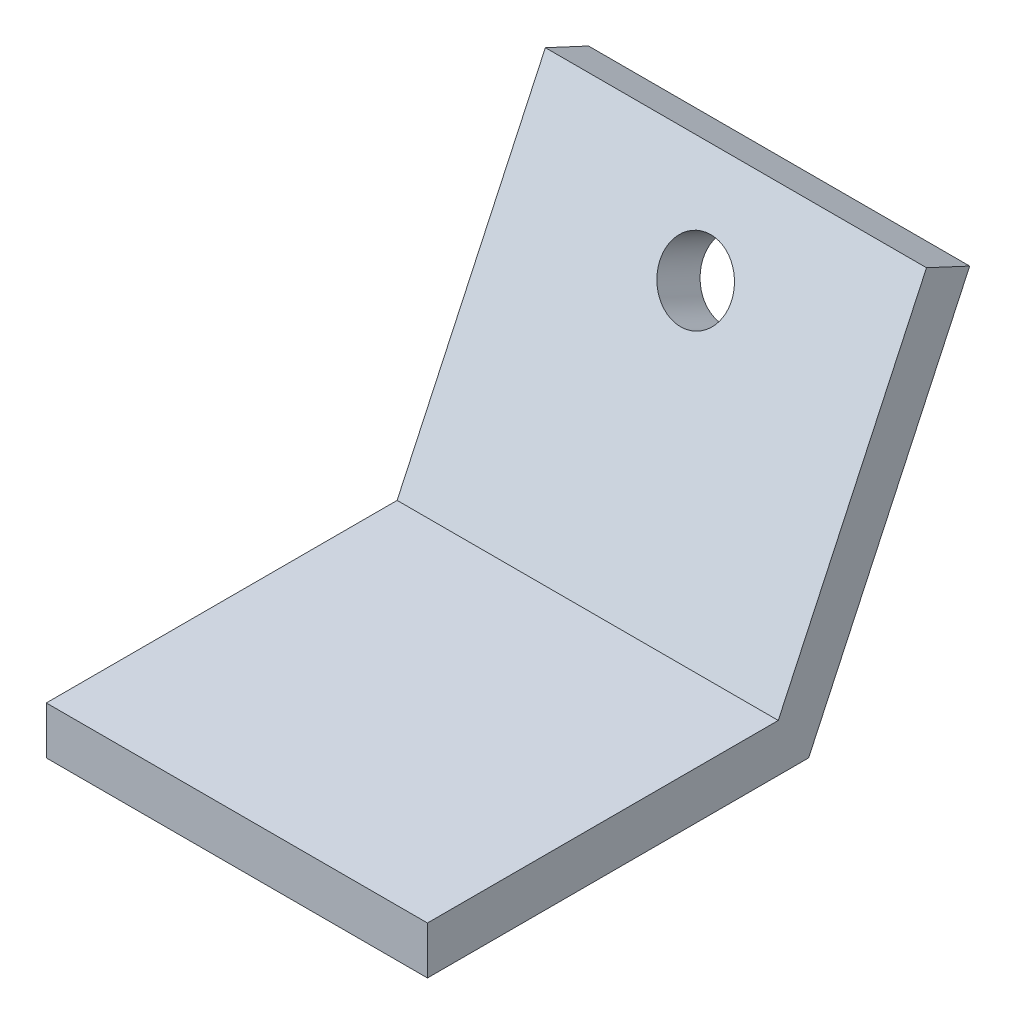
SolidWorks part; units mm, degrees
ref_plane "Front Plane" through (0, 0, 0) normal (0, 0, 1) x (1, 0, 0)
ref_plane "Top Plane" through (0, 0, 0) normal (0, 1, 0) x (1, 0, 0)
ref_plane "Right Plane" through (0, 0, 0) normal (1, 0, 0) x (0, 0, -1)
sketch "Sketch2" plane through (0, 0, 0) normal (1, 0, 0) x (0, 0, -1)
  line L0 (-25.4, 0) -> (25.4, 0)
  line L1 (25.4, 0) -> (46.869, 46.0404)
  line L2 (46.869, 46.0404) -> (41.114, 48.7241)
  line L3 (41.114, 48.7241) -> (21.3546, 6.35)
  line L4 (21.3546, 6.35) -> (-25.4, 6.35)
  line L5 (-25.4, 6.35) -> (-25.4, 0)
  point P4 (0, 0)
  dimension "D1" = 6.35
  dimension "D2" = 50.8
  dimension "D3" = 115
extrude "Boss-Extrude2" add sketch "Sketch2" along normal blind 50.8
sketch "Sketch3" plane through (0, -9.7288, -20.8634) normal (0, -0.4226, -0.9063) x (1, 0, 0)
  line L0 (25.4, -10.7345) -> (25.4, -48.8345) construction
  line L1 (50.8, -10.7345) -> (0, -10.7345) construction
  circle A0 centre (25.4, -48.8345) radius 4.7625
  dimension "D1" = 38.1
  dimension "D2" = 9.525
extrude "Cut-Extrude1" cut sketch "Sketch3" against normal up to next
sketch "Sketch4" plane through (0, 0, 0) normal (0, -1, 0) x (1, 0, 0)
  line L0 (25.4, 25.4) -> (25.4, 0) construction
  line L1 (50.8, 25.4) -> (0, 25.4) construction
  line L2 (25.4, 0) -> (0, 0) construction
  circle A0 centre (25.4, 0) radius 4.7625
  dimension "D1" = 9.525
extrude "Boss-Extrude3" add sketch "Sketch4" along normal blind 12.7
